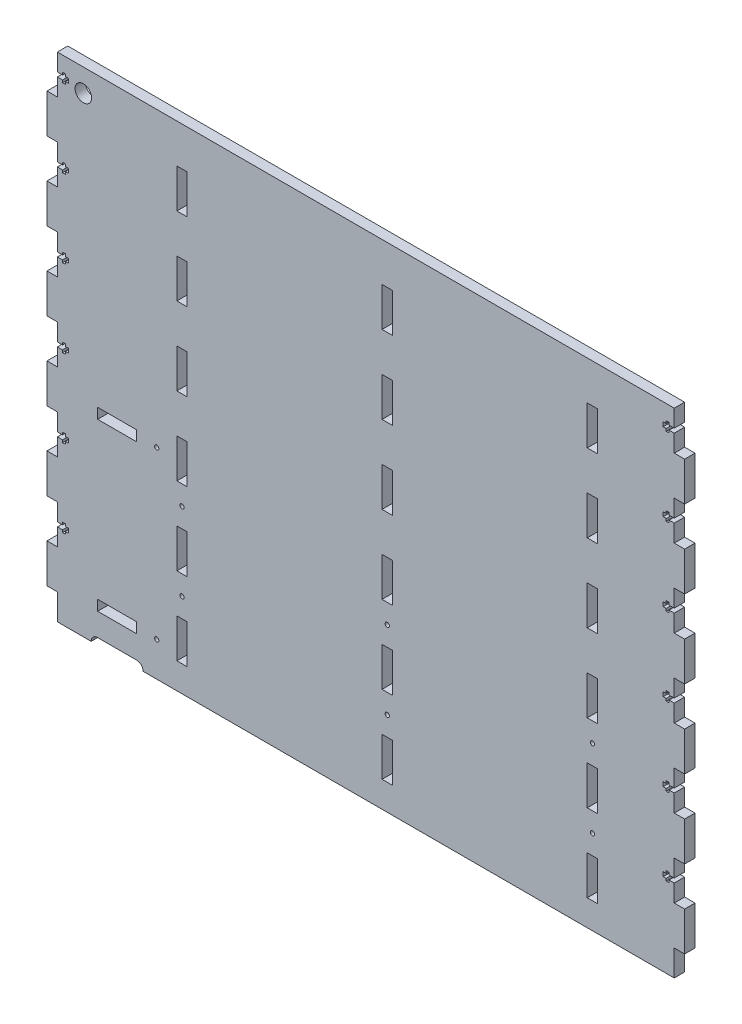
SolidWorks part; units mm, degrees
material "Acrylic (Medium-high impact)"
ref_plane "Front Plane" through (0, 0, 0) normal (0, 0, 1) x (1, 0, 0)
ref_plane "Top Plane" through (0, 0, 0) normal (0, 1, 0) x (1, 0, 0)
ref_plane "Right Plane" through (0, 0, 0) normal (1, 0, 0) x (0, 0, -1)
sketch "Sketch1" plane through (0, 0, 0) normal (0, 0, 1) x (1, 0, 0)
  line L0 (250, 350) -> (258, 350)
  line L1 (0, 0) -> (475, 0)
  line L2 (0, 380) -> (0, 0)
  line L3 (0, 380) -> (475, 380)
  line L4 (475, 0) -> (475, 380)
  line L5 (31, 158.5669) -> (61, 158.5669)
  line L6 (31, 158.5669) -> (31, 150.5669)
  line L7 (31, 150.5669) -> (61, 150.5669)
  line L8 (61, 158.5669) -> (61, 150.5669)
  line L9 (31, 30.5669) -> (61, 30.5669)
  line L10 (31, 30.5669) -> (31, 22.5669)
  line L11 (31, 22.5669) -> (61, 22.5669)
  line L12 (61, 30.5669) -> (61, 22.5669)
  line L13 (92, 350) -> (100, 350)
  line L14 (92, 350) -> (92, 320)
  line L15 (92, 320) -> (100, 320)
  line L16 (100, 350) -> (100, 320)
  line L17 (250, 350) -> (250, 320)
  line L18 (250, 320) -> (258, 320)
  line L19 (258, 350) -> (258, 320)
  line L20 (408, 350) -> (416, 350)
  line L21 (408, 350) -> (408, 320)
  line L22 (408, 320) -> (416, 320)
  line L23 (416, 350) -> (416, 320)
  line L24 (92, 290) -> (100, 290)
  line L25 (92, 290) -> (92, 260)
  line L26 (92, 260) -> (100, 260)
  line L27 (100, 290) -> (100, 260)
  line L28 (250, 290) -> (258, 290)
  line L29 (250, 290) -> (250, 260)
  line L30 (250, 260) -> (258, 260)
  line L31 (258, 290) -> (258, 260)
  line L32 (408, 290) -> (416, 290)
  line L33 (408, 290) -> (408, 260)
  line L34 (408, 260) -> (416, 260)
  line L35 (416, 290) -> (416, 260)
  line L36 (92, 230) -> (100, 230)
  line L37 (92, 230) -> (92, 200)
  line L38 (92, 200) -> (100, 200)
  line L39 (100, 230) -> (100, 200)
  line L40 (250, 230) -> (258, 230)
  line L41 (250, 230) -> (250, 200)
  line L42 (250, 200) -> (258, 200)
  line L43 (258, 230) -> (258, 200)
  line L44 (408, 230) -> (416, 230)
  line L45 (408, 230) -> (408, 200)
  line L46 (408, 200) -> (416, 200)
  line L47 (416, 230) -> (416, 200)
  line L48 (92, 170) -> (100, 170)
  line L49 (92, 170) -> (92, 140)
  line L50 (92, 140) -> (100, 140)
  line L51 (100, 170) -> (100, 140)
  line L52 (250, 170) -> (258, 170)
  line L53 (250, 170) -> (250, 140)
  line L54 (250, 140) -> (258, 140)
  line L55 (258, 170) -> (258, 140)
  line L56 (408, 170) -> (416, 170)
  line L57 (408, 170) -> (408, 140)
  line L58 (408, 140) -> (416, 140)
  line L59 (416, 170) -> (416, 140)
  line L60 (92, 110) -> (100, 110)
  line L61 (92, 110) -> (92, 80)
  line L62 (92, 80) -> (100, 80)
  line L63 (100, 110) -> (100, 80)
  line L64 (250, 110) -> (258, 110)
  line L65 (250, 110) -> (250, 80)
  line L66 (250, 80) -> (258, 80)
  line L67 (258, 110) -> (258, 80)
  line L68 (408, 110) -> (416, 110)
  line L69 (408, 110) -> (408, 80)
  line L70 (408, 80) -> (416, 80)
  line L71 (416, 110) -> (416, 80)
  line L72 (250, 110) -> (250, 80)
  line L73 (258, 110) -> (258, 80)
  line L74 (250, 110) -> (258, 110)
  line L75 (250, 80) -> (258, 80)
  line L76 (408, 110) -> (408, 80)
  line L77 (416, 110) -> (416, 80)
  line L78 (408, 110) -> (416, 110)
  line L79 (408, 80) -> (416, 80)
  line L80 (92, 50) -> (92, 20)
  line L81 (100, 50) -> (100, 20)
  line L82 (92, 50) -> (100, 50)
  line L83 (92, 20) -> (100, 20)
  line L84 (250, 50) -> (250, 20)
  line L85 (258, 50) -> (258, 20)
  line L86 (250, 50) -> (258, 50)
  line L87 (250, 20) -> (258, 20)
  line L88 (408, 50) -> (408, 20)
  line L89 (416, 50) -> (416, 20)
  line L90 (408, 50) -> (416, 50)
  line L91 (408, 20) -> (416, 20)
  line L146 (237.5, 0) -> (237.5, 380) construction
  circle A0 centre (20, 362.5) radius 6.35
  circle A1 centre (76.5, 154.5669) radius 1.65
  circle A2 centre (76.5, 26.5669) radius 1.65
  circle A3 centre (96, 125) radius 1.65
  circle A4 centre (254, 125) radius 1.65
  circle A5 centre (412, 125) radius 1.65
  circle A6 centre (96, 65) radius 1.65
  circle A7 centre (254, 65) radius 1.65
  circle A8 centre (412, 65) radius 1.65
  dimension "D4" = 5
  dimension "D6" = 92
  dimension "D3" = 3
  dimension "D5" = 30
  dimension "D9" = 15.5
  dimension "D10" = 3.3
  dimension "D12" = 3.3
  dimension "D13" = 12.7
  dimension "D1" = 475
  dimension "D2" = 380
  dimension "D7" = 30
  dimension "D8" = 8
  dimension "D11" = 15
  dimension "D14" = 17.5
  dimension "D15" = 20
  dimension "D16" = 3
  dimension "D17" = 2
extrude "Boss-Extrude1" add sketch "Sketch1" along normal blind 8 contours L1 L146 L3 L2 L60 L63 L62 L61 L36 L39 L38 L37 L13 L16 L15 L14 L5 L8 L7 L6 L9 L12 L11 L10 L24 L27 L26 L25 L48 L51 L50 L49 L83 L80 L82 L81 A0 A1 A2 | L146 L1 L4 L3 A8 A7 A5 A4 L91 L88 L90 L89 L87 L84 L86 L85 L64 L67 L66 L65 L56 L59 L58 L57 L40 L43 L42 L41 L32 L35 L34 L33 L0 L19 L18 L17 L20 L23 L22
sketch "Sketch2" plane through (0, 0, 8) normal (0, 0, 1) x (1, 0, 0)
  line L0 (483, 350) -> (475, 350)
  line L1 (0, 350) -> (-8, 350)
  line L2 (0, 350) -> (0, 320)
  line L3 (0, 320) -> (-8, 320)
  line L4 (-8, 350) -> (-8, 320)
  line L5 (475, 380) -> (0, 380) construction
  line L6 (483, 350) -> (483, 320)
  line L7 (483, 320) -> (475, 320)
  line L8 (475, 350) -> (475, 320)
  line L9 (0, 290) -> (-8, 290)
  line L10 (0, 290) -> (0, 260)
  line L11 (0, 260) -> (-8, 260)
  line L12 (-8, 290) -> (-8, 260)
  line L13 (483, 290) -> (475, 290)
  line L14 (483, 290) -> (483, 260)
  line L15 (483, 260) -> (475, 260)
  line L16 (475, 290) -> (475, 260)
  line L17 (0, 230) -> (-8, 230)
  line L18 (0, 230) -> (0, 200)
  line L19 (0, 200) -> (-8, 200)
  line L20 (-8, 230) -> (-8, 200)
  line L21 (483, 230) -> (475, 230)
  line L22 (237.5, 380) -> (237.5, 0) construction
  line L23 (0, 0) -> (475, 0) construction
  line L24 (483, 230) -> (483, 200)
  line L25 (483, 200) -> (475, 200)
  line L26 (475, 230) -> (475, 200)
  line L27 (0, 170) -> (-8, 170)
  line L28 (0, 170) -> (0, 140)
  line L29 (0, 140) -> (-8, 140)
  line L30 (-8, 170) -> (-8, 140)
  line L31 (483, 170) -> (475, 170)
  line L32 (483, 170) -> (483, 140)
  line L33 (483, 140) -> (475, 140)
  line L34 (475, 170) -> (475, 140)
  line L35 (0, 110) -> (-8, 110)
  line L36 (0, 110) -> (0, 80)
  line L37 (0, 80) -> (-8, 80)
  line L38 (-8, 110) -> (-8, 80)
  line L39 (483, 110) -> (475, 110)
  line L40 (483, 110) -> (483, 80)
  line L41 (483, 80) -> (475, 80)
  line L42 (475, 110) -> (475, 80)
  line L43 (0, 50) -> (-8, 50)
  line L44 (0, 50) -> (0, 20)
  line L45 (0, 20) -> (-8, 20)
  line L46 (-8, 50) -> (-8, 20)
  line L47 (483, 50) -> (475, 50)
  line L48 (483, 50) -> (483, 20)
  line L49 (483, 20) -> (475, 20)
  line L50 (475, 50) -> (475, 20)
  dimension "D1" = 30
  dimension "D2" = 30
  dimension "D3" = 8
extrude "Boss-Extrude2" add sketch "Sketch2" against normal blind 8
sketch "Sketch4" plane through (0, 0, 8) normal (0, 0, 1) x (1, 0, 0)
  line L0 (475, 366.65) -> (471, 366.65)
  line L1 (0, 65) -> (8.5, 65) construction
  line L2 (471, 366.65) -> (471, 368.5)
  line L3 (471, 368.5) -> (468.8, 368.5)
  line L4 (468.8, 368.5) -> (468.8, 366.65)
  line L5 (468.8, 366.65) -> (466.5, 366.65)
  line L6 (475, 365) -> (466.5, 365) construction
  line L7 (466.5, 366.65) -> (466.5, 363.35)
  line L8 (468.8, 363.35) -> (466.5, 363.35)
  line L9 (468.8, 361.5) -> (468.8, 363.35)
  line L10 (471, 361.5) -> (468.8, 361.5)
  line L11 (471, 363.35) -> (471, 361.5)
  line L12 (475, 363.35) -> (471, 363.35)
  line L13 (475, 366.65) -> (475, 363.35)
  line L14 (0, 125) -> (8.5, 125) construction
  line L15 (0, 185) -> (8.5, 185) construction
  line L16 (0, 245) -> (8.5, 245) construction
  line L17 (0, 305) -> (8.5, 305) construction
  line L18 (0, 365) -> (8.5, 365) construction
  line L19 (0, 66.65) -> (0, 63.35)
  line L20 (0, 63.35) -> (4, 63.35)
  line L21 (4, 63.35) -> (4, 61.5)
  line L22 (4, 61.5) -> (6.2, 61.5)
  line L23 (6.2, 61.5) -> (6.2, 63.35)
  line L24 (6.2, 63.35) -> (8.5, 63.35)
  line L25 (8.5, 66.65) -> (8.5, 63.35)
  line L26 (6.2, 66.65) -> (8.5, 66.65)
  line L27 (6.2, 68.5) -> (6.2, 66.65)
  line L28 (4, 68.5) -> (6.2, 68.5)
  line L29 (4, 66.65) -> (4, 68.5)
  line L30 (0, 66.65) -> (4, 66.65)
  line L31 (0, 126.65) -> (0, 123.35)
  line L32 (0, 123.35) -> (4, 123.35)
  line L33 (4, 123.35) -> (4, 121.5)
  line L34 (4, 121.5) -> (6.2, 121.5)
  line L35 (6.2, 121.5) -> (6.2, 123.35)
  line L36 (6.2, 123.35) -> (8.5, 123.35)
  line L37 (8.5, 126.65) -> (8.5, 123.35)
  line L38 (6.2, 126.65) -> (8.5, 126.65)
  line L39 (6.2, 128.5) -> (6.2, 126.65)
  line L40 (4, 128.5) -> (6.2, 128.5)
  line L41 (4, 126.65) -> (4, 128.5)
  line L42 (0, 126.65) -> (4, 126.65)
  line L43 (0, 186.65) -> (0, 183.35)
  line L44 (0, 183.35) -> (4, 183.35)
  line L45 (4, 183.35) -> (4, 181.5)
  line L46 (4, 181.5) -> (6.2, 181.5)
  line L47 (6.2, 181.5) -> (6.2, 183.35)
  line L48 (6.2, 183.35) -> (8.5, 183.35)
  line L49 (8.5, 186.65) -> (8.5, 183.35)
  line L50 (6.2, 186.65) -> (8.5, 186.65)
  line L51 (6.2, 188.5) -> (6.2, 186.65)
  line L52 (4, 188.5) -> (6.2, 188.5)
  line L53 (4, 186.65) -> (4, 188.5)
  line L54 (0, 186.65) -> (4, 186.65)
  line L55 (0, 246.65) -> (0, 243.35)
  line L56 (0, 243.35) -> (4, 243.35)
  line L57 (4, 243.35) -> (4, 241.5)
  line L58 (4, 241.5) -> (6.2, 241.5)
  line L59 (6.2, 241.5) -> (6.2, 243.35)
  line L60 (6.2, 243.35) -> (8.5, 243.35)
  line L61 (8.5, 246.65) -> (8.5, 243.35)
  line L62 (6.2, 246.65) -> (8.5, 246.65)
  line L63 (6.2, 248.5) -> (6.2, 246.65)
  line L64 (4, 248.5) -> (6.2, 248.5)
  line L65 (4, 246.65) -> (4, 248.5)
  line L66 (0, 246.65) -> (4, 246.65)
  line L67 (0, 306.65) -> (0, 303.35)
  line L68 (0, 303.35) -> (4, 303.35)
  line L69 (4, 303.35) -> (4, 301.5)
  line L70 (4, 301.5) -> (6.2, 301.5)
  line L71 (6.2, 301.5) -> (6.2, 303.35)
  line L72 (6.2, 303.35) -> (8.5, 303.35)
  line L73 (8.5, 306.65) -> (8.5, 303.35)
  line L74 (237.5, 380) -> (237.5, 0) construction
  line L75 (6.2, 306.65) -> (8.5, 306.65)
  line L76 (6.2, 308.5) -> (6.2, 306.65)
  line L77 (4, 308.5) -> (6.2, 308.5)
  line L78 (4, 306.65) -> (4, 308.5)
  line L79 (0, 306.65) -> (4, 306.65)
  line L80 (0, 366.65) -> (0, 363.35)
  line L81 (0, 363.35) -> (4, 363.35)
  line L82 (4, 363.35) -> (4, 361.5)
  line L83 (4, 361.5) -> (6.2, 361.5)
  line L84 (6.2, 361.5) -> (6.2, 363.35)
  line L85 (6.2, 363.35) -> (8.5, 363.35)
  line L86 (8.5, 366.65) -> (8.5, 363.35)
  line L87 (6.2, 366.65) -> (8.5, 366.65)
  line L88 (6.2, 368.5) -> (6.2, 366.65)
  line L89 (4, 368.5) -> (6.2, 368.5)
  line L90 (4, 366.65) -> (4, 368.5)
  line L91 (0, 366.65) -> (4, 366.65)
  line L150 (475, 350) -> (475, 380) construction
  line L151 (475, 380) -> (0, 380) construction
  line L152 (0, 0) -> (475, 0) construction
  line L160 (31, 0) -> (61, 0) construction
  line L161 (31, 5) -> (61, 5)
  line L162 (31, -5) -> (61, -5)
  line L163 (475, 306.65) -> (471, 306.65)
  line L164 (471, 306.65) -> (471, 308.5)
  line L165 (471, 308.5) -> (468.8, 308.5)
  line L166 (468.8, 308.5) -> (468.8, 306.65)
  line L167 (468.8, 306.65) -> (466.5, 306.65)
  line L168 (466.5, 306.65) -> (466.5, 303.35)
  line L169 (468.8, 303.35) -> (466.5, 303.35)
  line L170 (468.8, 301.5) -> (468.8, 303.35)
  line L171 (471, 301.5) -> (468.8, 301.5)
  line L172 (471, 303.35) -> (471, 301.5)
  line L173 (475, 303.35) -> (471, 303.35)
  line L174 (475, 306.65) -> (475, 303.35)
  line L175 (475, 305) -> (466.5, 305) construction
  line L176 (475, 246.65) -> (471, 246.65)
  line L177 (471, 246.65) -> (471, 248.5)
  line L178 (471, 248.5) -> (468.8, 248.5)
  line L179 (468.8, 248.5) -> (468.8, 246.65)
  line L180 (468.8, 246.65) -> (466.5, 246.65)
  line L181 (466.5, 246.65) -> (466.5, 243.35)
  line L182 (468.8, 243.35) -> (466.5, 243.35)
  line L183 (468.8, 241.5) -> (468.8, 243.35)
  line L184 (471, 241.5) -> (468.8, 241.5)
  line L185 (471, 243.35) -> (471, 241.5)
  line L186 (475, 243.35) -> (471, 243.35)
  line L187 (475, 246.65) -> (475, 243.35)
  line L188 (475, 245) -> (466.5, 245) construction
  line L189 (475, 186.65) -> (471, 186.65)
  line L190 (471, 186.65) -> (471, 188.5)
  line L191 (471, 188.5) -> (468.8, 188.5)
  line L192 (468.8, 188.5) -> (468.8, 186.65)
  line L193 (468.8, 186.65) -> (466.5, 186.65)
  line L194 (466.5, 186.65) -> (466.5, 183.35)
  line L195 (468.8, 183.35) -> (466.5, 183.35)
  line L196 (468.8, 181.5) -> (468.8, 183.35)
  line L197 (471, 181.5) -> (468.8, 181.5)
  line L198 (471, 183.35) -> (471, 181.5)
  line L199 (475, 183.35) -> (471, 183.35)
  line L200 (475, 186.65) -> (475, 183.35)
  line L201 (475, 185) -> (466.5, 185) construction
  line L202 (475, 126.65) -> (471, 126.65)
  line L203 (471, 126.65) -> (471, 128.5)
  line L204 (471, 128.5) -> (468.8, 128.5)
  line L205 (468.8, 128.5) -> (468.8, 126.65)
  line L206 (468.8, 126.65) -> (466.5, 126.65)
  line L207 (466.5, 126.65) -> (466.5, 123.35)
  line L208 (468.8, 123.35) -> (466.5, 123.35)
  line L209 (468.8, 121.5) -> (468.8, 123.35)
  line L210 (471, 121.5) -> (468.8, 121.5)
  line L211 (471, 123.35) -> (471, 121.5)
  line L212 (475, 123.35) -> (471, 123.35)
  line L213 (475, 126.65) -> (475, 123.35)
  line L214 (475, 125) -> (466.5, 125) construction
  line L215 (475, 66.65) -> (471, 66.65)
  line L216 (471, 66.65) -> (471, 68.5)
  line L217 (471, 68.5) -> (468.8, 68.5)
  line L218 (468.8, 68.5) -> (468.8, 66.65)
  line L219 (468.8, 66.65) -> (466.5, 66.65)
  line L220 (466.5, 66.65) -> (466.5, 63.35)
  line L221 (468.8, 63.35) -> (466.5, 63.35)
  line L222 (468.8, 61.5) -> (468.8, 63.35)
  line L223 (471, 61.5) -> (468.8, 61.5)
  line L224 (471, 63.35) -> (471, 61.5)
  line L225 (475, 63.35) -> (471, 63.35)
  line L226 (475, 66.65) -> (475, 63.35)
  line L227 (475, 65) -> (466.5, 65) construction
  arc A0 (31, 5) -> (31, -5) centre (31, 0) ccw
  arc A1 (61, -5) -> (61, 5) centre (61, 0) ccw
  point P178 (46, 0)
  dimension "D1" = 5
  dimension "D2" = 2.2
  dimension "D3" = 4
  dimension "D4" = 2.3
  dimension "D5" = 7
  dimension "D7" = 3.3
  dimension "D6" = 6
extrude "Cut-Extrude2" cut sketch "Sketch4" against normal through all
